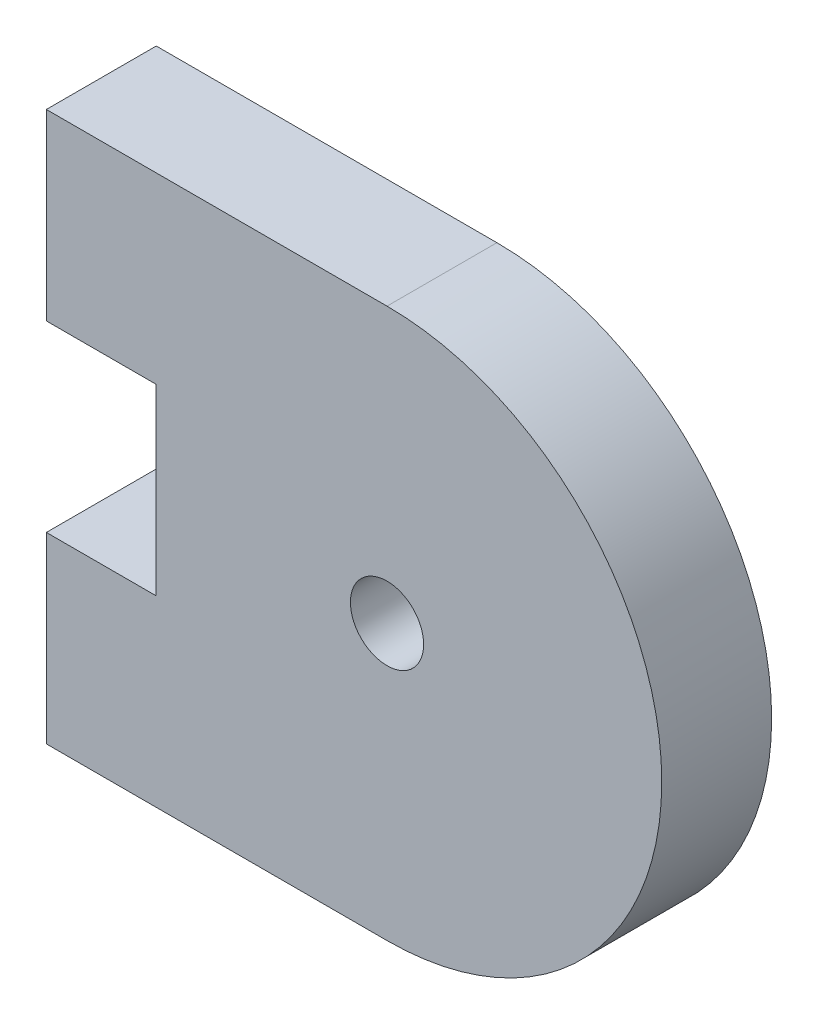
SolidWorks part; units mm, degrees
ref_plane "Alzado" through (0, 0, 0) normal (0, 0, 1) x (1, 0, 0)
ref_plane "Planta" through (0, 0, 0) normal (0, 1, 0) x (1, 0, 0)
ref_plane "Vista lateral" through (0, 0, 0) normal (1, 0, 0) x (0, 0, -1)
sketch "Corte exterior" plane through (0, 0, 0) normal (0, 0, 1) x (1, 0, 0)
  line L0 (42.4, 49.8786) -> (33.1, 49.8786)
  line L1 (33.1, 49.8786) -> (33.1, 44.8786)
  line L2 (33.1, 44.8786) -> (36.1, 44.8786)
  line L3 (36.1, 44.8786) -> (36.1, 39.8786)
  line L4 (36.1, 39.8786) -> (33.1, 39.8786)
  line L5 (33.1, 39.8786) -> (33.1, 34.8786)
  line L6 (33.1, 34.8786) -> (42.4, 34.8786)
  circle A0 centre (42.4, 42.3786) radius 1
  arc A1 (42.4, 34.8786) -> (42.4, 49.8786) centre (42.4, 42.3786) ccw
sketch "Grabado Superficie" plane through (0, 0, 0) normal (0, 0, 1) x (1, 0, 0)
  circle A0 centre (42.4, 42.3786) radius 2.15
extrude "Saliente-Extruir1" add sketch "Corte exterior" along normal blind 3
extrude "Cortar-Extruir1" cut sketch "Grabado Superficie" along normal blind 1
